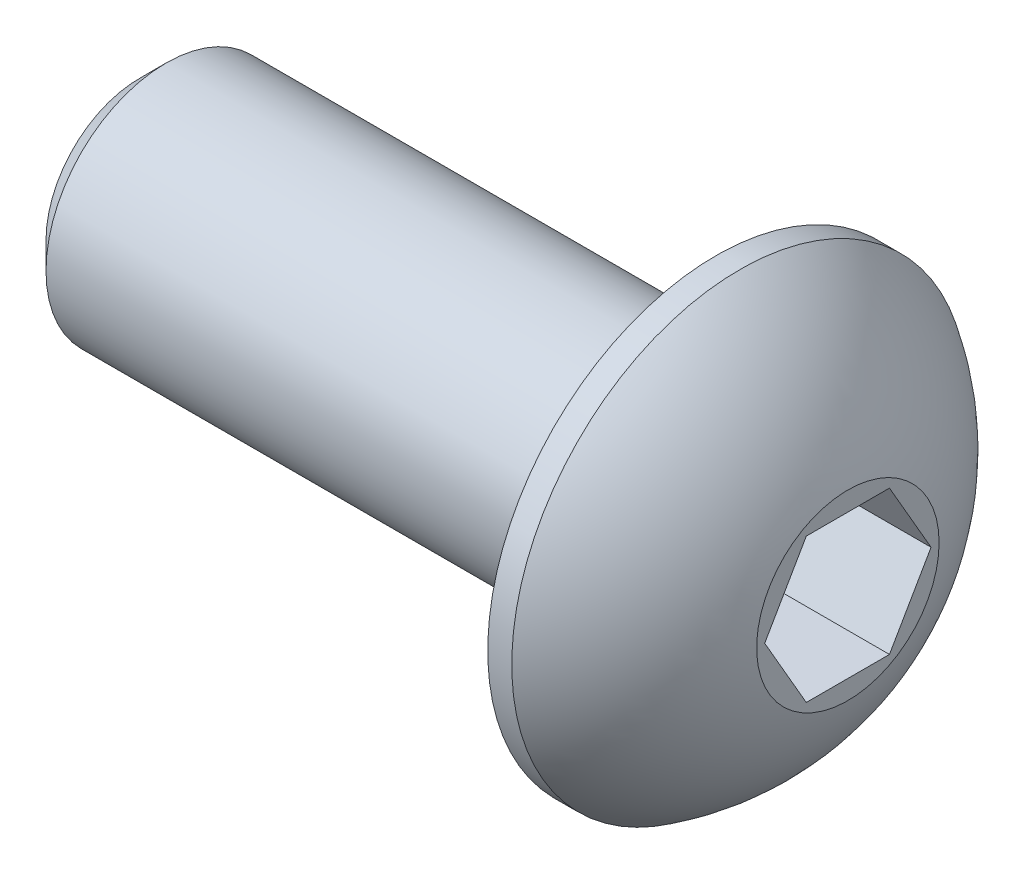
SolidWorks part; units mm, degrees
ref_plane "Front Plane" through (0, 0, 0) normal (0, 0, 1) x (1, 0, 0)
ref_plane "Top Plane" through (0, 0, 0) normal (0, 1, 0) x (1, 0, 0)
ref_plane "Right Plane" through (0, 0, 0) normal (1, 0, 0) x (0, 0, -1)
ref_plane "Plane1" through (0, 0, 9.9) normal (0, 0, 1) x (1, 0, 0)
sketch "Sketch1" plane through (0, 0, 9.9) normal (0, 0, 1) x (1, 0, 0)
  line L0 (2.4, 14.65) -> (2.4, 9.9)
  line L1 (2.4, 9.9) -> (5.15, 9.9)
  line L2 (5.15, 9.9) -> (5.15, 11.8)
  line L3 (2.9, 14.65) -> (2.4, 14.65)
  line L4 (2.4, 9.9) -> (5.15, 9.9) construction
  arc A0 (5.15, 11.8) -> (2.9, 14.65) centre (0.2005, 10.2056) ccw
revolve "Revolve1" add sketch "Sketch1" angle 360 about L4
sketch "Sketch2" plane through (2.4, 0, 0) normal (-1, 0, 0) x (0, 0, 1)
  circle A0 centre (9.9, 9.9) radius 2.5
extrude "Boss-Extrude1" add sketch "Sketch2" along normal blind 12
sketch "Sketch3" plane through (5.15, 0, 0) normal (1, 0, 0) x (0, 0, -1)
  line L0 (-11.6321, 9.9) -> (-10.766, 8.4)
  line L1 (-10.766, 8.4) -> (-9.034, 8.4)
  line L2 (-9.034, 8.4) -> (-8.1679, 9.9)
  line L3 (-8.1679, 9.9) -> (-9.034, 11.4)
  line L4 (-9.034, 11.4) -> (-10.766, 11.4)
  line L5 (-10.766, 11.4) -> (-11.6321, 9.9)
extrude "Cut-Extrude1" cut sketch "Sketch3" against normal blind 2.2
chamfer "Chamfer1" distance 0.55 angle 45 1 edges at (-9.6, 9.9, 12.4)
chamfer "Chamfer2" distance 0.35 angle 59.744 1 edges at (2.4, 9.9, 12.4)
